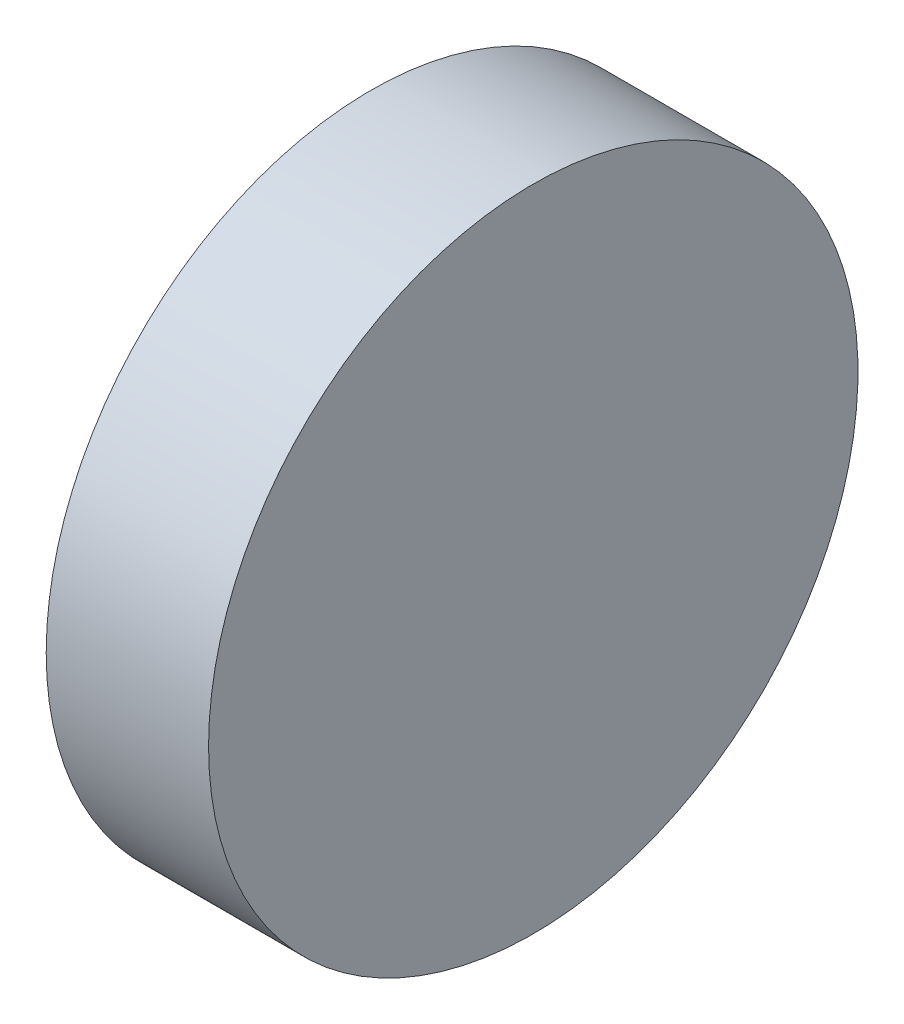
SolidWorks part; units mm, degrees
ref_plane "前视基准面" through (0, 0, 0) normal (0, 0, 1) x (1, 0, 0)
ref_plane "上视基准面" through (0, 0, 0) normal (0, 1, 0) x (1, 0, 0)
ref_plane "右视基准面" through (0, 0, 0) normal (1, 0, 0) x (0, 0, -1)
sketch "草图1" plane through (0, 0, 0) normal (0, 1, 0) x (1, 0, 0)
  line L0 (-5.443, 0) -> (14.3524, 0) construction
  line L1 (0, 0) -> (6.35, 0)
  line L2 (0, 0) -> (0, -12.7)
  line L3 (0, -12.7) -> (6.35, -12.7)
  line L4 (6.35, 0) -> (6.35, -12.7)
  dimension "D1" = 6.35
  dimension "D2" = 12.7
revolve "旋转1" add sketch "草图1" angle 360 about L0
